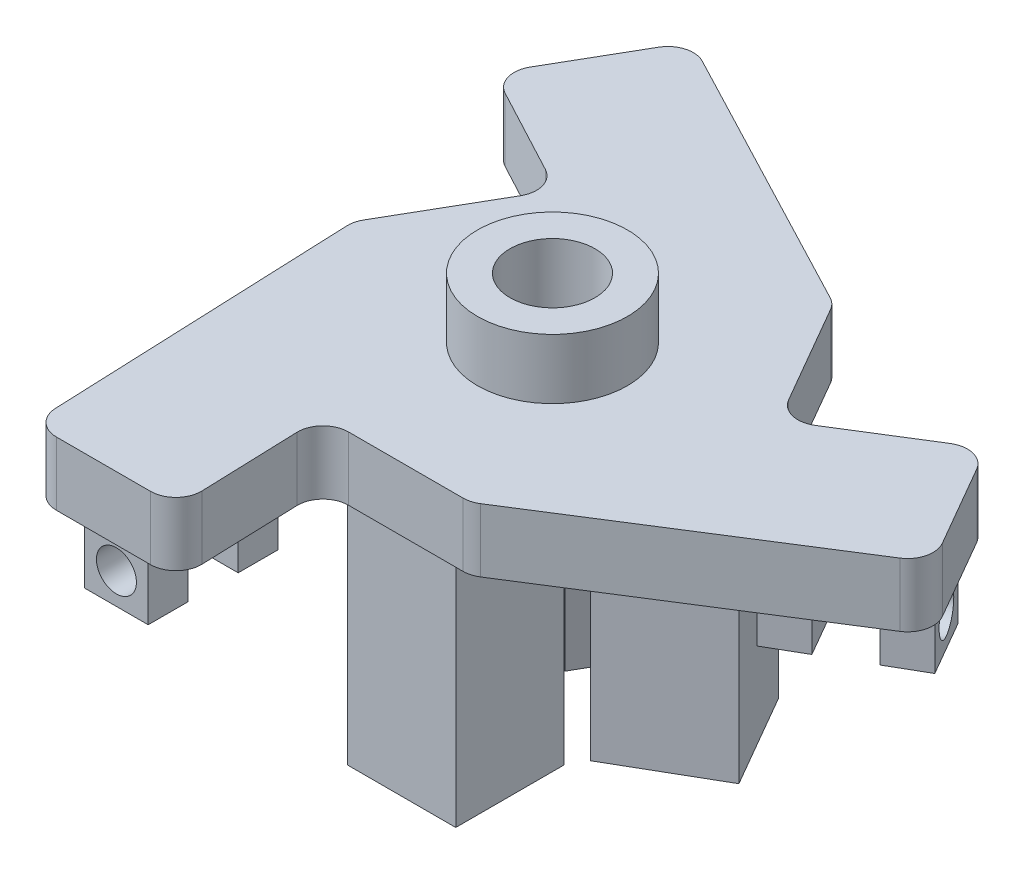
SolidWorks part; units mm, degrees
ref_plane "Front Plane" through (0, 0, 0) normal (0, 0, 1) x (1, 0, 0)
ref_plane "Top Plane" through (0, 0, 0) normal (0, 1, 0) x (1, 0, 0)
ref_plane "Right Plane" through (0, 0, 0) normal (1, 0, 0) x (0, 0, -1)
sketch "Sketch1" plane through (0, 0, 0) normal (0, 1, 0) x (1, 0, 0)
  line L1 (19.05, -32.9956) -> (38.1, 0)
  line L2 (38.1, 0) -> (19.05, 32.9956)
  line L3 (19.05, 32.9956) -> (-19.05, 32.9956)
  line L4 (-19.05, 32.9956) -> (-38.1, 0)
  line L5 (-38.1, 0) -> (-19.05, -32.9956)
  line L6 (-19.05, -32.9956) -> (19.05, -32.9956)
  circle A0 centre (0, 0) radius 32.9956 construction
  dimension "D1" = 38.1
extrude "Boss-Extrude1" add sketch "Sketch1" along normal blind 6.35 contours L4 L5 L6 L1 L2 L3
sketch "Sketch2" plane through (0, 0, 0) normal (0, -1, 0) x (1, 0, 0)
  line L0 (-5.425, 15.1) -> (-5.425, 4.25)
  line L5 (-3.425, 13.1) -> (3.425, 13.1)
  line L6 (-3.425, 13.1) -> (-3.425, 6.25)
  line L7 (-3.425, 6.25) -> (3.425, 6.25)
  line L8 (3.425, 13.1) -> (3.425, 6.25)
  line L9 (-3.425, 13.1) -> (3.425, 6.25) construction
  line L10 (-3.425, 6.25) -> (3.425, 13.1) construction
  line L11 (-5.425, 4.25) -> (-2.067, 4.25)
  line L12 (5.425, 15.1) -> (5.425, 4.25)
  line L13 (-5.425, 15.1) -> (5.425, 15.1)
  line L14 (2.067, 4.25) -> (5.425, 4.25)
  line L15 (-5.425, 4.25) -> (5.425, 4.25) construction
  line L16 (13.0574, -3.5839) -> (7.1252, -0.1589)
  line L17 (13.0574, -3.5839) -> (9.6324, -9.5161)
  line L18 (9.6324, -9.5161) -> (3.7002, -6.0911)
  line L19 (7.1252, -0.1589) -> (3.7002, -6.0911)
  line L20 (2.6471, -3.9151) -> (0.9681, -6.8232)
  line L21 (10.3645, -12.2482) -> (0.9681, -6.8232)
  line L22 (15.7895, -2.8518) -> (10.3645, -12.2482)
  line L23 (15.7895, -2.8518) -> (6.3931, 2.5732)
  line L24 (6.3931, 2.5732) -> (4.7141, -0.3349)
  line L25 (-9.6324, -9.5161) -> (-3.7002, -6.0911)
  line L26 (-9.6324, -9.5161) -> (-13.0574, -3.5839)
  line L27 (-13.0574, -3.5839) -> (-7.1252, -0.1589)
  line L28 (-3.7002, -6.0911) -> (-7.1252, -0.1589)
  line L29 (-4.7141, -0.3349) -> (-6.3931, 2.5732)
  line L30 (-15.7895, -2.8518) -> (-6.3931, 2.5732)
  line L31 (-10.3645, -12.2482) -> (-15.7895, -2.8518)
  line L32 (-10.3645, -12.2482) -> (-0.9681, -6.8232)
  line L33 (-0.9681, -6.8232) -> (-2.6471, -3.9151)
  circle A0 centre (0, 0) radius 4.726 construction
  arc A2 (-2.067, 4.25) -> (2.067, 4.25) centre (0, 0) cw
  arc A3 (4.7141, -0.3349) -> (2.6471, -3.9151) centre (0, 0) cw
  arc A4 (-2.6471, -3.9151) -> (-4.7141, -0.3349) centre (0, 0) cw
  point P3 (0, 9.675)
  point P37 (0, 0)
  dimension "D1" = 9.675
  dimension "D3" = 1.524
  dimension "D4" = 2
  dimension "D2" = 6.85
  dimension "D5" = 3
sketch "Sketch6" plane through (0, 6.35, 0) normal (0, 1, 0) x (1, 0, 0)
  circle A0 centre (0, 0) radius 4.25
  dimension "D1" = 8.5
extrude "Cut-Extrude1" cut sketch "Sketch6" against normal through all
extrude "Boss-Extrude2" add sketch "Sketch2" along normal blind 25.4
sketch "Sketch7" plane through (0, 0, 0) normal (0, -1, 0) x (1, 0, 0)
  line L0 (-14.8153, 22.9723) -> (-8.4653, 22.9723)
  line L1 (-8.4653, 22.9723) -> (-8.4653, 18.9723)
  line L2 (-8.4653, 18.9723) -> (-14.8153, 18.9723)
  line L3 (-14.8153, 18.9723) -> (-14.8153, 22.9723)
  line L4 (-19.05, -32.9956) -> (-38.1, 0) construction
  line L5 (-19.05, 32.9956) -> (19.05, 32.9956) construction
  line L6 (38.1, 0) -> (19.05, -32.9956) construction
  line L7 (-14.8153, 27.9723) -> (-14.8153, 31.9723)
  line L8 (-14.8153, 31.9723) -> (-8.4653, 31.9723)
  line L9 (-8.4653, 31.9723) -> (-8.4653, 27.9723)
  line L10 (-8.4653, 27.9723) -> (-14.8153, 27.9723)
  line L11 (-5.425, 15.1) -> (-5.425, 4.25) construction
  line L12 (27.2966, 1.354) -> (24.1216, -4.1453)
  line L13 (24.1216, -4.1453) -> (20.6575, -2.1453)
  line L14 (20.6575, -2.1453) -> (23.8325, 3.354)
  line L15 (23.8325, 3.354) -> (27.2966, 1.354)
  line L16 (31.6268, -1.146) -> (35.0909, -3.146)
  line L17 (35.0909, -3.146) -> (31.9159, -8.6453)
  line L18 (31.9159, -8.6453) -> (28.4518, -6.6453)
  line L19 (28.4518, -6.6453) -> (31.6268, -1.146)
  line L20 (-12.4813, -24.3068) -> (-15.6563, -18.8076)
  line L21 (-15.6563, -18.8076) -> (-12.1922, -16.8076)
  line L22 (-12.1922, -16.8076) -> (-9.0172, -22.3068)
  line L23 (-9.0172, -22.3068) -> (-12.4813, -24.3068)
  line L24 (-16.8115, -26.8068) -> (-20.2756, -28.8068)
  line L25 (-20.2756, -28.8068) -> (-23.4506, -23.3076)
  line L26 (-23.4506, -23.3076) -> (-19.9865, -21.3076)
  line L27 (-19.9865, -21.3076) -> (-16.8115, -26.8068)
  point P13 (-11.6403, 18.9723)
  dimension "D1" = 22.9723
  dimension "D2" = 4
  dimension "D4" = 5
  dimension "D5" = 6.2153
  dimension "D6" = 6.35
  dimension "D8" = 1.033
  dimension "D9" = 1.033
  dimension "D3" = 2
  dimension "D7" = 3
extrude "Boss-Extrude3" add sketch "Sketch7" along normal blind 6.35
sketch "Sketch9" plane through (0, 0, 31.9723) normal (0, 0, 1) x (1, 0, 0)
  line L0 (-8.4653, -6.35) -> (-14.8153, -6.35) construction
  line L1 (-19.05, 0) -> (19.05, 0) construction
  circle A0 centre (-11.6403, -3.2626) radius 2
  point P4 (-11.6403, -6.35)
  dimension "D1" = 4
  dimension "D2" = 3.2626
extrude "Cut-Extrude2" cut sketch "Sketch9" against normal blind 6.54
pattern_circular "CirPattern1" count 3 over 360 about axis through (0, 0, 0) along (0, 1, 0) of "Cut-Extrude2"
sketch "Sketch10" plane through (0, 0, 22.9723) normal (0, 0, 1) x (1, 0, 0)
  circle A0 centre (-11.6403, -3.2626) radius 1.7145
  dimension "D1" = 3.429
extrude "Cut-Extrude3" cut sketch "Sketch10" against normal blind 2
pattern_circular "CirPattern2" count 3 over 360 about axis through (0, 0, 0) along (0, 1, 0) of "Cut-Extrude3"
sketch "Sketch11" plane through (0, 0, 0) normal (0, -1, 0) x (1, 0, 0)
  line L0 (-38.1, 0) -> (-19.05, 32.9956)
  line L1 (-19.05, -32.9956) -> (-38.1, 0) construction
  line L2 (-38.1, 0) -> (-19.05, 32.9956) construction
  line L5 (-20.4169, -0.5354) -> (-12.9994, -13.3828)
  line L6 (-12.9994, -13.3828) -> (-26.2859, -20.4626)
  line L7 (-26.2859, -20.4626) -> (-38.1, 0)
  line L21 (-19.05, 32.9956) -> (-20.4169, -0.5354)
  line L22 (19.05, 32.9956) -> (38.1, 0)
  line L23 (9.7447, 17.9492) -> (-5.0901, 17.9492)
  line L24 (-5.0901, 17.9492) -> (-4.5782, 32.9956)
  line L25 (-4.5782, 32.9956) -> (19.05, 32.9956)
  line L26 (38.1, 0) -> (9.7447, 17.9492)
  line L27 (19.05, -32.9956) -> (-19.05, -32.9956)
  line L28 (10.6721, -17.4138) -> (18.0896, -4.5665)
  line L29 (18.0896, -4.5665) -> (30.8641, -12.533)
  line L30 (30.8641, -12.533) -> (19.05, -32.9956)
  line L31 (-19.05, -32.9956) -> (10.6721, -17.4138)
  point P21 (0, 0)
  dimension "D1" = 3
extrude "Cut-Extrude4" cut sketch "Sketch11" against normal up to surface (6.35 mm away) up to face at (0, 6.35, 4.25)
fillet "Fillet1" radius 2.54 12 edges at (18.0896, 3.175, -4.5665) (-12.9994, 3.175, -13.3828) (-5.0901, 3.175, 17.9492) (-19.05, 3.175, 32.9956) (-4.5782, 3.175, 32.9956) (-26.2859, 3.175, -20.4626) (-19.05, 3.175, -32.9956) (30.8641, 3.175, -12.533) (38.1, 3.175, 0) (9.7447, 3.175, 17.9492) (-20.4169, 3.175, -0.5354) (10.6721, 3.175, -17.4138)
sketch "Sketch12" plane through (0, 6.35, 0) normal (0, 1, 0) x (1, 0, 0)
  circle A0 centre (0, 0) radius 7.5
  circle A1 centre (0, 0) radius 4.25
  dimension "D1" = 15
  dimension "D2" = 8.5
extrude "Boss-Extrude4" add sketch "Sketch12" along normal blind 6
